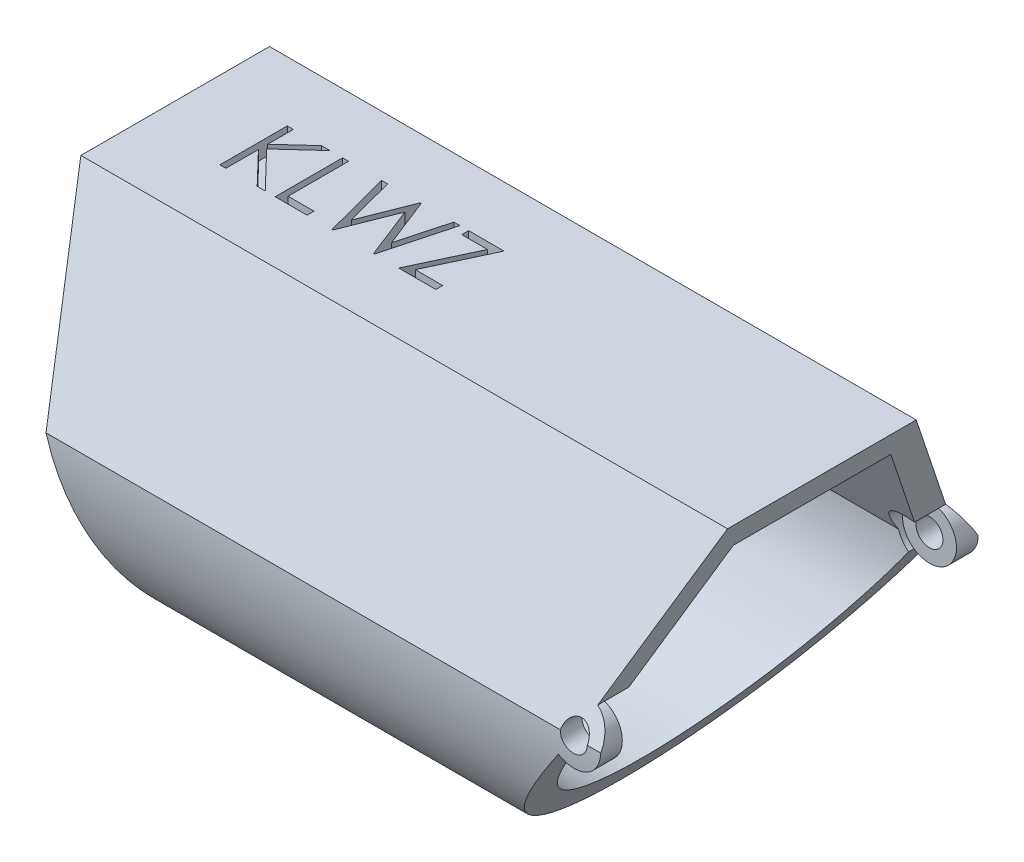
SolidWorks part; units mm, degrees
material "1060 Alloy"
ref_plane "Front Plane" through (0, 0, 0) normal (0, 0, 1) x (1, 0, 0)
ref_plane "Top Plane" through (0, 0, 0) normal (0, 1, 0) x (1, 0, 0)
ref_plane "Right Plane" through (0, 0, 0) normal (1, 0, 0) x (0, 0, -1)
sketch "Sketch1" plane through (0, 0, 0) normal (1, 0, 0) x (0, 0, -1)
  line L0 (-4.445, 0) -> (4.445, 0)
  line L1 (4.445, 0) -> (8.89, -7.699)
  line L2 (-4.445, 0) -> (-8.89, -7.699)
  arc A1 (-8.89, -7.699) -> (8.89, -7.699) centre (0, -8.207) ccw
  point P6 (0, 0)
  dimension "D1" = 120
  dimension "D3" = 8.89
  dimension "D2" = 120
  dimension "D4" = 0.508
extrude "Boss-Extrude1" add sketch "Sketch1" along normal blind 30.48
shell "Shell1" thickness 1.27
sketch "Sketch2" plane through (0, 0, 0) normal (0, 0, 1) x (1, 0, 0)
  line L0 (30.48, 0) -> (28.1122, -6.5056)
  line L1 (30.48, -7.699) -> (0, -7.699) construction
  line L2 (26.9494, -8.7393) -> (21.0871, -17.1115)
  line L3 (0, -17.1115) -> (30.48, -17.1115) construction
  line L4 (30.48, 0) -> (0, 0) construction
  line L5 (30.48, 0) -> (30.48, -17.1115)
  line L6 (30.48, -17.1115) -> (21.0871, -17.1115)
  line L7 (0, -17.1115) -> (30.48, -17.1115) construction
  line L8 (0, -17.1115) -> (6.2281, -17.1115)
  line L9 (0, 0) -> (0, -17.1115)
  line L12 (0, 0) -> (0, -7.699) construction
  line L13 (0, -7.699) -> (0, -17.1115) construction
  line L14 (0, 0) -> (6.2281, -17.1115)
  arc A0 (28.1122, -6.5056) -> (26.9494, -8.7393) centre (27.6778, -7.699) cw
  circle A1 centre (27.6778, -7.699) radius 0.635
  dimension "D4" = 1.27
  dimension "D5" = 1.27
  dimension "D1" = 70
  dimension "D2" = 55
  dimension "D3" = 70
extrude "Cut-Extrude1" cut sketch "Sketch2" against normal through all both and the other way through all
ref_plane "Plane1" through (27.6778, 0, 0) normal (1, 0, 0) x (0, 0, -1)
sketch "Sketch4" plane through (27.6778, 0, 0) normal (1, 0, 0) x (0, 0, -1)
  line L0 (-6.7345, -6.5056) -> (-8.201, -6.5056) construction
  line L1 (-7.874, -6.5056) -> (-6.4553, -6.5056)
  line L2 (-7.874, -6.5056) -> (-7.874, -8.969)
  line L3 (-7.874, -8.969) -> (-6.4553, -8.969)
  line L4 (-6.4553, -6.5056) -> (-6.4553, -8.969)
  line L5 (-8.8718, -8.969) -> (-7.5964, -8.969) construction
  line L6 (0, -10.5518) -> (0, -5.2635) construction
  line L8 (6.4553, -6.5056) -> (6.4553, -8.969)
  line L9 (7.874, -8.969) -> (6.4553, -8.969)
  line L10 (7.874, -6.5056) -> (7.874, -8.969)
  line L11 (7.874, -6.5056) -> (6.4553, -6.5056)
  dimension "D1" = 7.874
sketch "Sketch5" plane through (0, 0, 0) normal (0, 0, 1) x (1, 0, 0)
  circle A0 centre (27.6778, -7.699) radius 1.27
  dimension "D1" = 2.54
extrude "Cut-Extrude3" cut sketch "Sketch5" against normal blind 7.874 and the other way blind 7.874
ref_plane "Plane2" through (0, -17.1115, 0) normal (0, 1, 0) x (1, 0, 0)
sketch "Sketch6" plane through (0, -17.1115, 0) normal (0, 1, 0) x (1, 0, 0)
  line L0 (27.0428, -8.89) -> (2.8022, -8.89) construction
  line L1 (5.0295, -1.27) -> (6.9901, -1.27)
  line L2 (5.0295, -1.27) -> (5.0295, 1.27)
  line L3 (5.0295, 1.27) -> (6.9901, 1.27)
  line L4 (6.9901, -1.27) -> (6.9901, 1.27)
  line L5 (6.2281, -7.6084) -> (6.2281, 6.1874) construction
  ellipse E1 centre (2.9871, 0) end of major axis (2.9871, -8.9045) minor radius 3.241 (2.8022, -8.89) -> (2.8022, 8.89) ccw construction
  dimension "D1" = 2.54
  dimension "D2" = 7.62
  dimension "D3" = 0.762
extrude "Cut-Extrude4" cut sketch "Sketch6" along normal blind 0.508
sketch "Sketch3" plane through (0, 0, 0) normal (0, 1, 0) x (1, 0, 0)
  text T0 "KLWZ" font "Century Gothic" height in points 12
extrude "Cut-Extrude2" cut sketch "Sketch3" against normal blind 0.762
